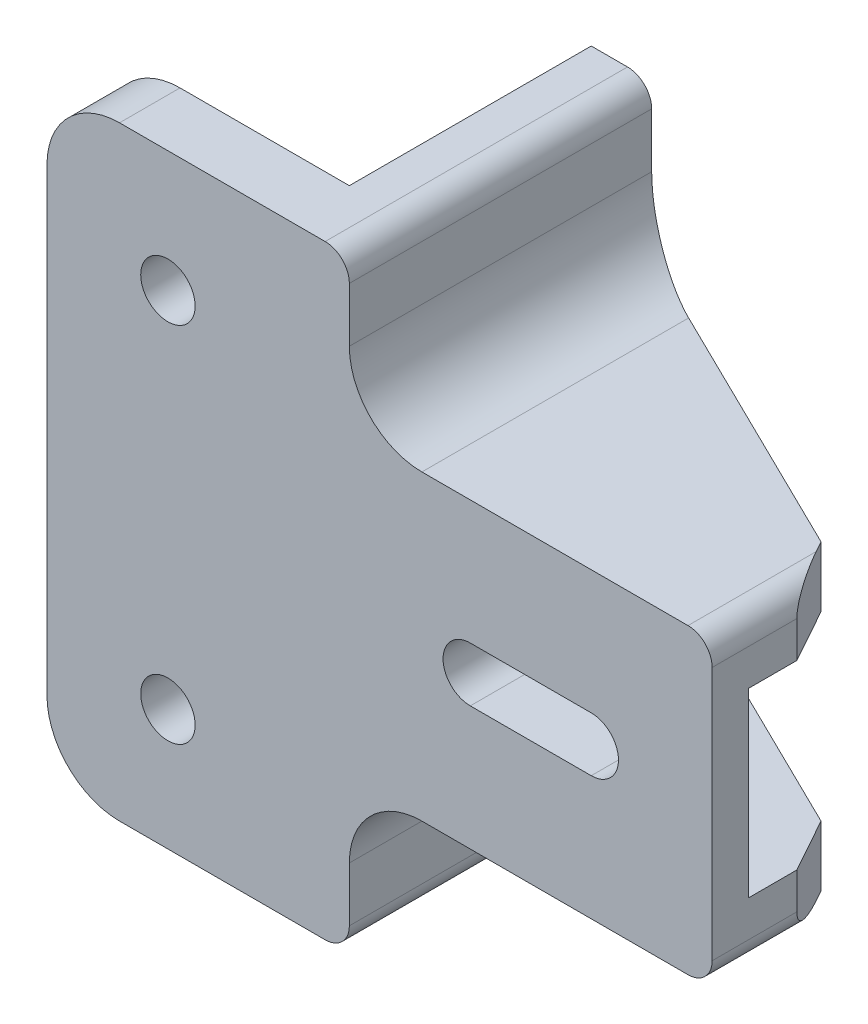
SolidWorks part; units mm, degrees
ref_plane "Front Plane" through (0, 0, 0) normal (0, 0, 1) x (1, 0, 0)
ref_plane "Top Plane" through (0, 0, 0) normal (0, 1, 0) x (1, 0, 0)
ref_plane "Right Plane" through (0, 0, 0) normal (1, 0, 0) x (0, 0, -1)
sketch "Sketch1" plane through (0, 0, 0) normal (0, 0, 1) x (1, 0, 0)
  line L0 (0, 25) -> (0, 0)
  line L1 (0, 25) -> (-30, 25)
  line L2 (-30, 25) -> (-30, 37.5)
  line L3 (-30, 37.5) -> (-55, 37.5)
  line L4 (-55, 37.5) -> (-55, -12.5)
  line L5 (-55, -12.5) -> (-30, -12.5)
  line L6 (-30, -12.5) -> (-30, 0)
  line L7 (-30, 0) -> (0, 0)
  dimension "D1" = 25
  dimension "D2" = 30
  dimension "D3" = 50
  dimension "D4" = 25
extrude "Boss-Extrude1" add sketch "Sketch1" along normal blind 5
sketch "Sketch2" plane through (0, 0, 5) normal (0, 0, 1) x (1, 0, 0)
  line L0 (0, 12.5) -> (-55, 12.5) construction
  line L1 (0, 0) -> (0, 25) construction
  line L2 (-55, 37.5) -> (-55, -12.5) construction
  line L3 (-10, 12.5) -> (-20, 12.5) construction
  line L4 (-10, 10.25) -> (-20, 10.25)
  line L5 (-10, 14.75) -> (-20, 14.75)
  line L6 (-55, 37.5) -> (-55, -12.5) construction
  arc A0 (-10, 10.25) -> (-10, 14.75) centre (-10, 12.5) ccw
  arc A1 (-20, 14.75) -> (-20, 10.25) centre (-20, 12.5) ccw
  circle A2 centre (-45, -2.5) radius 2.25
  circle A3 centre (-45, 27.5) radius 2.25
  point P8 (-15, 12.5)
  dimension "D1" = 4.5
  dimension "D4" = 14.5
  dimension "D6" = 25.5
  dimension "D2" = 4.5
  dimension "D3" = 7.75
  dimension "D5" = 10
extrude "Cut-Extrude1" cut sketch "Sketch2" against normal through all
sketch "Sketch3" plane through (0, 0, 0) normal (0, 0, -1) x (-1, 0, 0)
  line L0 (30, 37.5) -> (55, 37.5) construction
  line L1 (30, -12.5) -> (35, -12.5)
  line L2 (30, -12.5) -> (30, 37.5)
  line L3 (30, 37.5) -> (35, 37.5)
  line L4 (35, -12.5) -> (35, 37.5)
  dimension "D1" = 5
extrude "Boss-Extrude2" add sketch "Sketch3" along normal blind 20
sketch "Sketch4" plane through (-35, 0, 0) normal (-1, 0, 0) x (0, 0, 1)
  line L0 (-20, 12.5) -> (0, 12.5) construction
  line L1 (-20, -12.5) -> (-20, 37.5) construction
  line L2 (0, -12.5) -> (0, 37.5) construction
  circle A0 centre (-10, 12.5) radius 2.25
  dimension "D1" = 4.5
  dimension "D2" = 10
extrude "Cut-Extrude2" cut sketch "Sketch4" against normal through all
sketch "Sketch5" plane through (0, 0, 0) normal (1, 0, 0) x (0, 0, -1)
  line L0 (0, 12.5) -> (-5, 12.5) construction
  line L1 (0, 0) -> (0, 25) construction
  line L2 (-5, 0) -> (-5, 25) construction
  line L3 (0, 25) -> (20, 25)
  line L4 (20, 25) -> (20, 20)
  line L5 (20, 20) -> (0, 20)
  line L6 (0, 20) -> (0, 25)
  line L7 (20, 37.5) -> (20, -12.5) construction
  line L8 (20, 0) -> (20, 5)
  line L9 (0, 0) -> (20, 0)
  line L10 (0, 5) -> (0, 0)
  line L11 (20, 5) -> (0, 5)
  dimension "D1" = 5
extrude "Boss-Extrude3" add sketch "Sketch5" against normal blind 30
sketch "Sketch6" plane through (0, 25, 0) normal (0, 1, 0) x (1, 0, 0)
  line L0 (-30, 20) -> (0, 20)
  line L1 (0, 20) -> (0, 2)
  line L2 (0, -5) -> (0, 20) construction
  line L3 (0, 2) -> (-2.5, 6.5)
  line L4 (-2.5, 6.5) -> (-30, 20)
  dimension "D1" = 2
  dimension "D2" = 4.5
  dimension "D3" = 2.5
extrude "Cut-Extrude3" cut sketch "Sketch6" against normal through all
fillet "Fillet1" radius 6 2 edges at (-30, 0, -7.5) (-30, 25, -7.5)
chamfer "Chamfer1" distance 2 angle 45 2 edges at (0, 12.5, 0) (-30, 12.5, 0)
fillet "Fillet2" radius 6 2 edges at (-55, -12.5, 2.5) (-55, 37.5, 2.5)
fillet "Fillet3" radius 2 4 edges at (-30, 37.5, -7.5) (-30, -12.5, -7.5) (0, 25, 1.5) (0, 0, 1.5)
